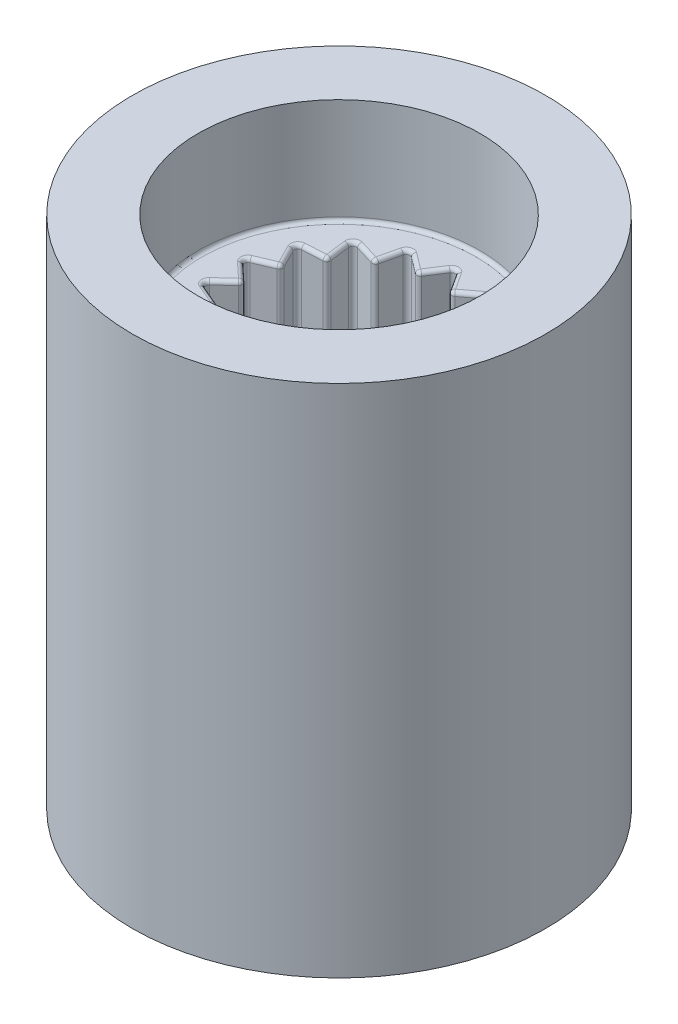
SolidWorks part; units mm, degrees
ref_plane "前视基准面" through (0, 0, 0) normal (0, 0, 1) x (1, 0, 0)
ref_plane "上视基准面" through (0, 0, 0) normal (0, 1, 0) x (1, 0, 0)
ref_plane "右视基准面" through (0, 0, 0) normal (1, 0, 0) x (0, 0, -1)
sketch "Sketch2" plane through (0, 0, 0) normal (0, 1, 0) x (1, 0, 0)
  circle A0 centre (0, 0) radius 5.5
  circle A1 centre (0, 0) radius 3.75
extrude "Boss-Extrude1" add sketch "Sketch2" along normal blind 13.7
sketch "Sketch3" plane through (0, 0, 0) normal (0, 1, 0) x (1, 0, 0)
  line L0 (0, 0) -> (0, 3.1672) construction
  line L1 (0, 0) -> (0.5965, 3.3826) construction
  line L2 (1.0833, 2.9762) -> (0, 0) construction
  line L3 (0, 3.1672) -> (0.4391, 2.4901)
  line L4 (1.0833, 2.9762) -> (0.4391, 2.4901)
  line L5 (1.0833, 2.9762) -> (1.2643, 2.1898)
  line L6 (2.0359, 2.4262) -> (1.2643, 2.1898)
  line L7 (2.0359, 2.4262) -> (1.937, 1.6253)
  line L8 (2.7429, 1.5836) -> (1.937, 1.6253)
  line L9 (2.7429, 1.5836) -> (2.3761, 0.8648)
  line L10 (3.1191, 0.55) -> (2.3761, 0.8648)
  line L11 (3.1191, 0.55) -> (2.5286, 0)
  line L12 (3.1191, -0.55) -> (2.5286, 0)
  line L13 (3.1191, -0.55) -> (2.3761, -0.8648)
  line L14 (2.7429, -1.5836) -> (2.3761, -0.8648)
  line L15 (2.7429, -1.5836) -> (1.937, -1.6253)
  line L16 (2.0359, -2.4262) -> (1.937, -1.6253)
  line L17 (2.0359, -2.4262) -> (1.2643, -2.1898)
  line L18 (1.0833, -2.9762) -> (1.2643, -2.1898)
  line L19 (1.0833, -2.9762) -> (0.4391, -2.4901)
  line L20 (0, -3.1672) -> (0.4391, -2.4901)
  line L21 (0, -3.1672) -> (-0.4391, -2.4901)
  line L22 (-1.0833, -2.9762) -> (-0.4391, -2.4901)
  line L23 (-1.0833, -2.9762) -> (-1.2643, -2.1898)
  line L24 (-2.0359, -2.4262) -> (-1.2643, -2.1898)
  line L25 (-2.0359, -2.4262) -> (-1.937, -1.6253)
  line L26 (-2.7429, -1.5836) -> (-1.937, -1.6253)
  line L27 (-2.7429, -1.5836) -> (-2.3761, -0.8648)
  line L28 (-3.1191, -0.55) -> (-2.3761, -0.8648)
  line L29 (-3.1191, -0.55) -> (-2.5286, 0)
  line L30 (-3.1191, 0.55) -> (-2.5286, 0)
  line L31 (-3.1191, 0.55) -> (-2.3761, 0.8648)
  line L32 (-2.7429, 1.5836) -> (-2.3761, 0.8648)
  line L33 (-2.7429, 1.5836) -> (-1.937, 1.6253)
  line L34 (-2.0359, 2.4262) -> (-1.937, 1.6253)
  line L35 (-2.0359, 2.4262) -> (-1.2643, 2.1898)
  line L36 (-1.0833, 2.9762) -> (-1.2643, 2.1898)
  line L37 (-1.0833, 2.9762) -> (-0.4391, 2.4901)
  line L38 (0, 3.1672) -> (-0.4391, 2.4901)
  circle A0 centre (0, 0) radius 4.6077
  circle A2 centre (0, 0) radius 2.6 construction
  point P8 (0, 0)
  point P12 (0, 0)
  point P15 (0, 0)
  point P18 (0, 0)
  point P21 (0, 0)
  point P24 (0, 0)
  point P27 (0, 0)
  point P30 (0, 0)
  point P33 (0, 0)
  point P36 (0, 0)
  point P39 (0, 0)
  point P42 (0, 0)
  point P45 (0, 0)
  point P48 (0, 0)
  point P51 (0, 0)
  point P54 (0, 0)
  point P57 (0, 0)
  point P60 (0, 0)
  point P61 (0, 0)
extrude "Boss-Extrude2" add sketch "Sketch3" along normal offset from surface (10.9 mm away) 2.8 up to face at (0, 13.7, 5.5)
fillet "Fillet1" radius 0.1 75 edges at (1.9864, 10.9, -2.0258) (1.9864, 0, -2.0258) (1.6501, 10.9, -2.308) (1.6501, 0, -2.308) (1.2643, 5.45, -2.1898) (2.0359, 5.45, -2.4262) (0, 10.9, 3.75) (0.2195, 10.9, -2.8287) (-0.2195, 10.9, -2.8287) (-0.7612, 10.9, -2.7332) (-1.1738, 10.9, -2.583) (-1.6501, 10.9, -2.308) (-1.9864, 10.9, -2.0258) (-2.3399, 10.9, -1.6045) (-2.5595, 10.9, -1.2242) (-2.7476, 10.9, -0.7074) (-2.8238, 10.9, -0.275) (-2.8238, 10.9, 0.275) (-2.7476, 10.9, 0.7074) (-2.5595, 10.9, 1.2242) (-2.3399, 10.9, 1.6045) (-1.9864, 10.9, 2.0258) (-1.6501, 10.9, 2.308) (-1.1738, 10.9, 2.583) (-0.7612, 10.9, 2.7332) (-0.2195, 10.9, 2.8287) (0.2195, 10.9, 2.8287) (0.7612, 10.9, 2.7332) (1.1738, 10.9, 2.583) (1.6501, 10.9, 2.308) (1.9864, 10.9, 2.0258) (2.3399, 10.9, 1.6045) (2.5595, 10.9, 1.2242) (2.7476, 10.9, 0.7074) (2.8238, 10.9, 0.275) (2.8238, 10.9, -0.275) (2.7476, 10.9, -0.7074) (2.5595, 10.9, -1.2242) (2.3399, 10.9, -1.6045) (1.1738, 10.9, -2.583) (0.7612, 10.9, -2.7332) (-2.3761, 5.45, -0.8648) (-3.1191, 5.45, -0.55) (-2.5286, 5.45, 0) (-3.1191, 5.45, 0.55) (-2.3761, 5.45, 0.8648) (-2.7429, 5.45, 1.5836) (-1.937, 5.45, 1.6253) (-2.0359, 5.45, 2.4262) (-1.0833, 5.45, 2.9762) (-1.2643, 5.45, 2.1898) (-0.4391, 5.45, 2.4901) (0, 5.45, 3.1672) (0.4391, 5.45, 2.4901) (1.0833, 5.45, 2.9762) (2.0359, 5.45, 2.4262) (1.2643, 5.45, 2.1898) (2.7429, 5.45, 1.5836) (1.937, 5.45, 1.6253) (2.3761, 5.45, 0.8648) (3.1191, 5.45, 0.55) (2.5286, 5.45, 0) (3.1191, 5.45, -0.55) (2.7429, 5.45, -1.5836) (2.3761, 5.45, -0.8648) (1.937, 5.45, -1.6253) (1.0833, 5.45, -2.9762) (0.4391, 5.45, -2.4901) (0, 5.45, -3.1672) (-0.4391, 5.45, -2.4901) (-1.0833, 5.45, -2.9762) (-1.2643, 5.45, -2.1898) (-2.0359, 5.45, -2.4262) (-1.937, 5.45, -1.6253) (-2.7429, 5.45, -1.5836)
